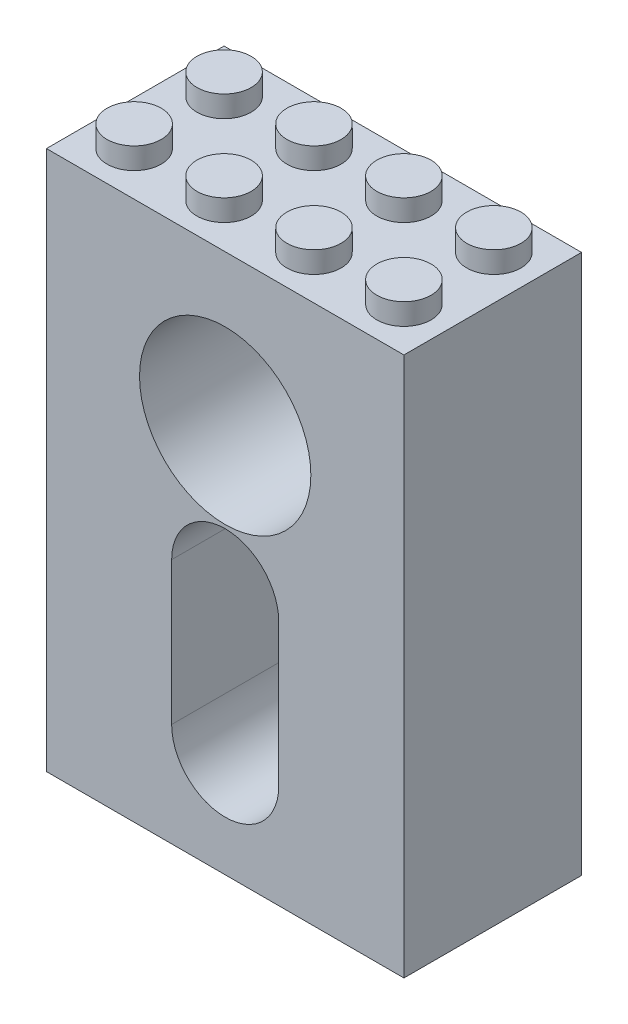
SolidWorks part; units mm, degrees
ref_plane "Front Plane" through (0, 0, 0) normal (0, 0, 1) x (1, 0, 0)
ref_plane "Top Plane" through (0, 0, 0) normal (0, 1, 0) x (1, 0, 0)
ref_plane "Right Plane" through (0, 0, 0) normal (1, 0, 0) x (0, 0, -1)
sketch "Sketch1" plane through (0, 0, 0) normal (0, 0, 1) x (1, 0, 0)
  line L1 (-15.9, 24) -> (15.9, 24)
  line L2 (-15.9, 24) -> (-15.9, -24)
  line L3 (-15.9, -24) -> (15.9, -24)
  line L4 (15.9, 24) -> (15.9, -24)
  line L5 (-15.9, 24) -> (15.9, -24) construction
  line L6 (-15.9, -24) -> (15.9, 24) construction
  point P0 (0, 0)
  dimension "D1" = 48
  dimension "D2" = 31.8
extrude "Boss-Extrude1" add sketch "Sketch1" along normal blind 15.8
sketch "Sketch2" plane through (0, 0, 15.8) normal (0, 0, 1) x (1, 0, 0)
  line L0 (0, -2.1) -> (0, -14.8) construction
  line L1 (4.7625, -2.1) -> (4.7625, -14.8)
  line L2 (-4.7625, -2.1) -> (-4.7625, -14.8)
  line L4 (15.9, 24) -> (-15.9, 24) construction
  line L5 (15.9, -24) -> (15.9, 24) construction
  circle A0 centre (0, 10.6) radius 7.62
  arc A1 (4.7625, -2.1) -> (-4.7625, -2.1) centre (0, -2.1) ccw
  arc A2 (-4.7625, -14.8) -> (4.7625, -14.8) centre (0, -14.8) ccw
  point P5 (0, -8.45)
  dimension "D1" = 4.7625
  dimension "D4" = 15.24
  dimension "D2" = 12.7
  dimension "D3" = 12.7
  dimension "D5" = 13.4
  dimension "D6" = 15.9
extrude "Cut-Extrude1" cut sketch "Sketch2" against normal blind 12.7
sketch "Sketch3" plane through (0, 0, 0) normal (0, 0, -1) x (-1, 0, 0)
  circle A6 centre (0, 10.6) radius 2.7782
  circle A7 centre (0, -2.1) radius 1.8415
  circle A8 centre (0, -14.8) radius 1.8415
  dimension "D1" = 5.5563
  dimension "D2" = 3.683
  dimension "D3" = 3.683
extrude "Cut-Extrude2" cut sketch "Sketch3" against normal blind 12.7
sketch "Sketch4" plane through (0, 0, 0) normal (0, 0, -1) x (-1, 0, 0)
  line L2 (4.7625, -14.8) -> (4.7625, -2.1)
  line L3 (-4.7625, -2.1) -> (-4.7625, -14.8)
  line L12 (4.7625, -14.8) -> (4.7625, -2.1)
  line L13 (-4.7625, -2.1) -> (-4.7625, -14.8)
  arc A2 (4.7625, -2.1) -> (-4.7625, -2.1) centre (0, -2.1) ccw
  arc A3 (-4.7625, -14.8) -> (4.7625, -14.8) centre (0, -14.8) ccw
  arc A4 (4.7625, -2.1) -> (-4.7625, -2.1) centre (0, -2.1) ccw
  arc A5 (-4.7625, -14.8) -> (4.7625, -14.8) centre (0, -14.8) ccw
  dimension "D2" = 0
extrude "Cut-Extrude3" cut sketch "Sketch4" against normal blind 1.905
sketch "Sketch5" plane through (0, 24, 0) normal (0, 1, 0) x (1, 0, 0)
  line L0 (15.9, -15.8) -> (-15.9, -15.8) construction
  line L1 (-15.9, -15.8) -> (-15.9, 0) construction
  circle A0 centre (-12, -3.9) radius 2.41
  circle A1 centre (-12, -11.9) radius 2.41
  circle A2 centre (-4, -3.9) radius 2.41
  circle A3 centre (-4, -11.9) radius 2.41
  circle A4 centre (4, -3.9) radius 2.41
  circle A5 centre (4, -11.9) radius 2.41
  circle A6 centre (12, -3.9) radius 2.41
  circle A7 centre (12, -11.9) radius 2.41
  dimension "D2" = 4.82
  dimension "D3" = 4.82
  dimension "D1" = 8
  dimension "D4" = 3.9
  dimension "D5" = 3.9
  dimension "D6" = 3.9
  dimension "D7" = 4
extrude "Boss-Extrude2" add sketch "Sketch5" along normal blind 1.905
sketch "Sketch6" plane through (0, -24, 0) normal (0, -1, 0) x (1, 0, 0)
  line L0 (-15.9, 15.8) -> (-15.9, 0) construction
  line L1 (-14.68, 14.58) -> (14.68, 14.58)
  line L2 (-14.68, 14.58) -> (-14.68, 1.22)
  line L3 (-14.68, 1.22) -> (14.68, 1.22)
  line L4 (14.68, 14.58) -> (14.68, 1.22)
  line L5 (15.9, 15.8) -> (15.9, 0) construction
  line L6 (-15.9, 0) -> (15.9, 0) construction
  line L7 (-15.9, 15.8) -> (15.9, 15.8) construction
  circle A0 centre (-8, 7.9) radius 3.26
  circle A1 centre (0, 7.9) radius 3.26
  circle A2 centre (8, 7.9) radius 3.26
  dimension "D6" = 6.52
  dimension "D1" = 1.22
  dimension "D2" = 1.22
  dimension "D3" = 1.22
  dimension "D4" = 1.22
  dimension "D5" = 7.9
  dimension "D7" = 7.9
  dimension "D8" = 3
extrude "Cut-Extrude4" cut sketch "Sketch6" against normal blind 1.905
